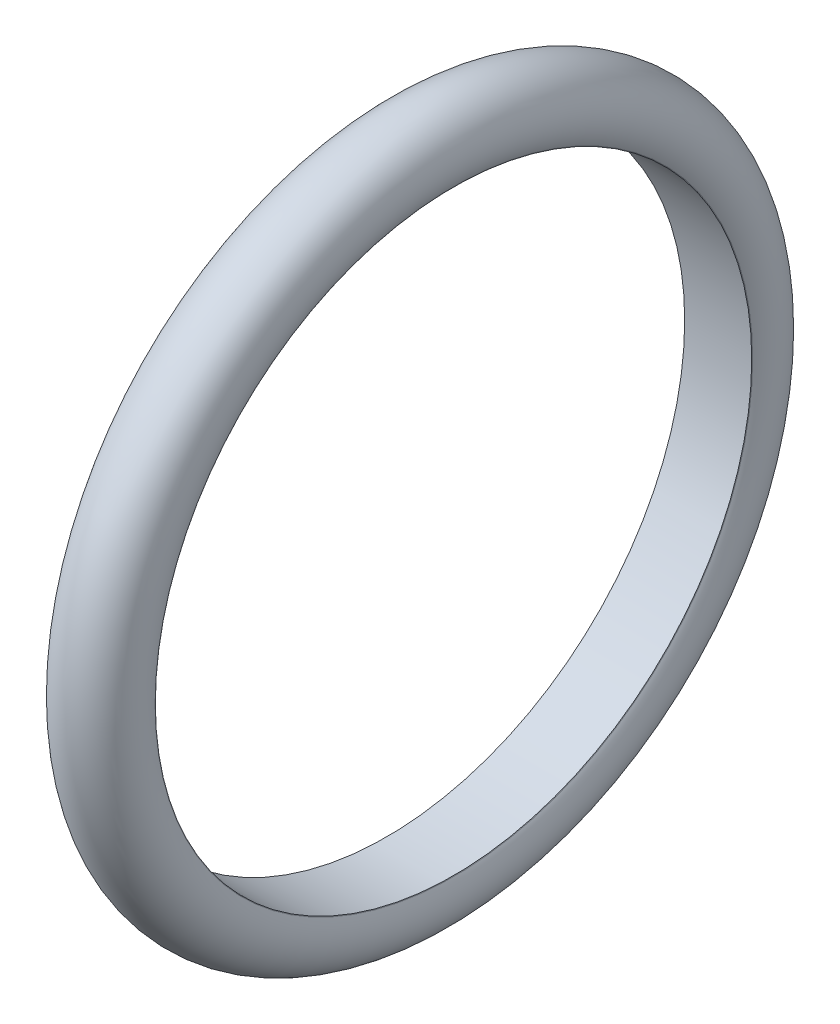
SolidWorks part; units mm, degrees
ref_plane "Front" through (0, 0, 0) normal (0, 0, 1) x (1, 0, 0)
ref_plane "Top" through (0, 0, 0) normal (0, 1, 0) x (1, 0, 0)
ref_plane "Right" through (0, 0, 0) normal (1, 0, 0) x (0, 0, -1)
sketch "Sketch1" plane through (0, 0, 0) normal (0, 0, 1) x (1, 0, 0)
  line L0 (-19.2474, 169.8625) -> (-19.05, 169.5206)
  line L1 (-19.05, 169.5206) -> (19.05, 169.5206)
  line L2 (19.05, 169.5206) -> (19.2474, 169.8625)
  line L3 (0, 0) -> (157.1582, 0) construction
  arc A0 (-19.2474, 169.8625) -> (19.2474, 169.8625) centre (0, 180.975) cw
  point P8 (0, 169.5206)
  dimension "D2" = 22.225
  dimension "D1" = 38.1
  dimension "D3" = 120
  dimension "D4" = 361.95
revolve "Revolve1" add sketch "Sketch1" angle 360 about L3
